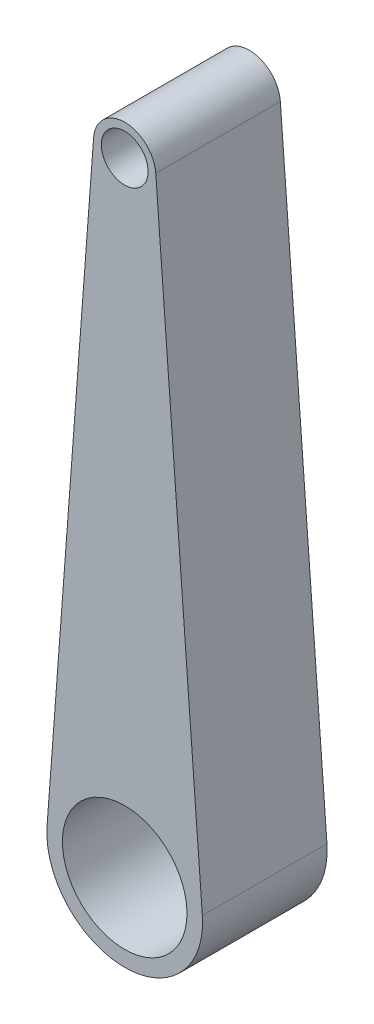
SolidWorks part; units mm, degrees
ref_plane "Ön Düzlem" through (0, 0, 0) normal (0, 0, 1) x (1, 0, 0)
ref_plane "Üst Düzlem" through (0, 0, 0) normal (0, 1, 0) x (1, 0, 0)
ref_plane "Sağ Düzlem" through (0, 0, 0) normal (1, 0, 0) x (0, 0, -1)
sketch "Çizim1" plane through (0, 0, 0) normal (0, 0, 1) x (1, 0, 0)
  line L0 (-2.493, 0.1875) -> (-0.9972, 20.075)
  line L1 (2.493, 0.1875) -> (0.9972, 20.075)
  circle A0 centre (0, 0) radius 2
  circle A1 centre (0, 0) radius 2.5
  arc A2 (0.9972, 20.075) -> (-0.9972, 20.075) centre (0, 20) ccw
  circle A3 centre (0, 20) radius 0.75
  dimension "D1" = 4
  dimension "D2" = 5
  dimension "D3" = 2
  dimension "D5" = 1.5
  dimension "D4" = 20
extrude "Yükseklik-Ekstrüzyon1" add sketch "Çizim1" along normal mid plane 4 contours L1 A2 L0 A1 A3 | A1 A0
